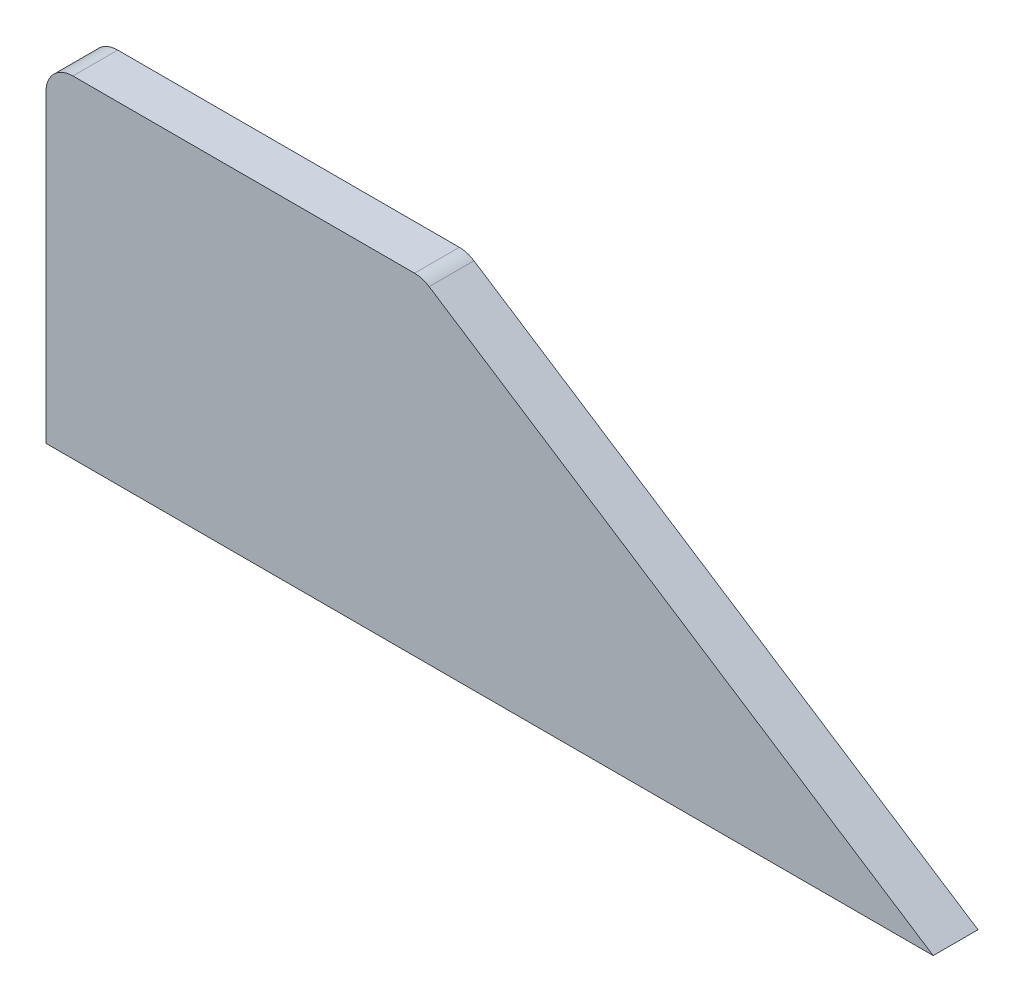
SolidWorks part; units mm, degrees
ref_plane "Alzado" through (0, 0, 0) normal (0, 0, 1) x (1, 0, 0)
ref_plane "Planta" through (0, 0, 0) normal (0, 1, 0) x (1, 0, 0)
ref_plane "Vista lateral" through (0, 0, 0) normal (1, 0, 0) x (0, 0, -1)
sketch "Croquis1" plane through (0, 0, 0) normal (0, 0, 1) x (1, 0, 0)
  point P0 (0, 0)
  line B0 (0, 0) -> (98.975, 0)
  line B1 (98.975, 0) -> (42.7453, 36.516)
  line B2 (0, 0) -> (0, 34)
  line B3 (3, 37) -> (41.1114, 37)
  arc B4 (0, 34) -> (3, 37) centre (3, 34) cw
  arc B5 (41.1114, 37) -> (42.7453, 36.516) centre (41.1114, 34) cw
sketch_block_instance "Bloque1-1"
sketch_block "Bloque1"
extrude "Saliente-Extruir1" add sketch "Croquis1" along normal blind 5
